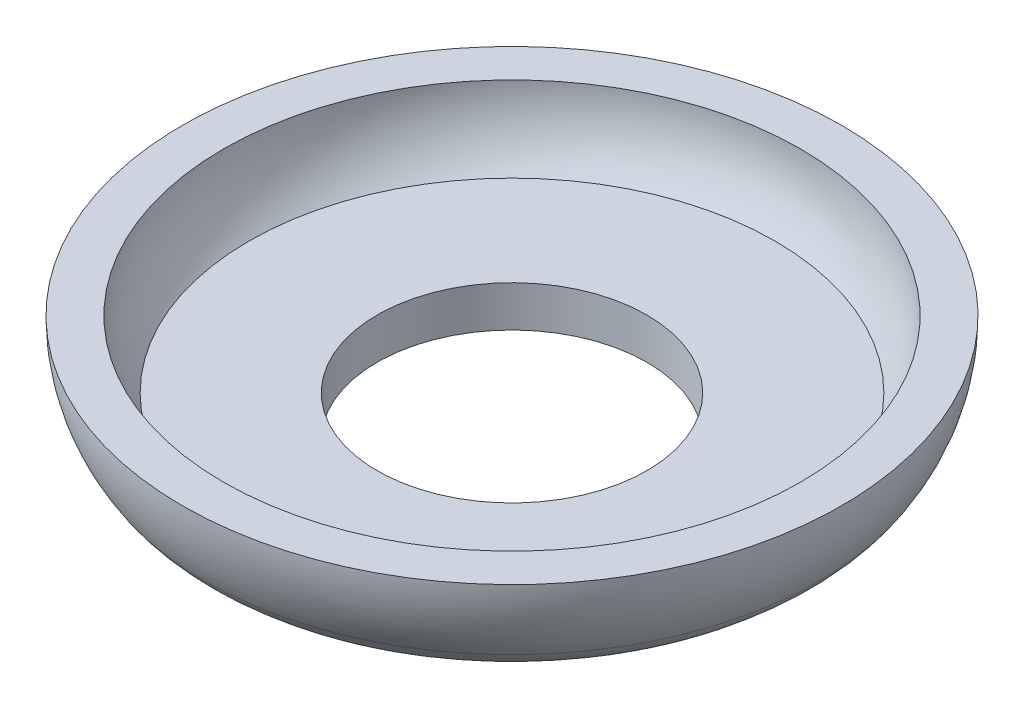
SolidWorks part; units mm, degrees
material "Cast Carbon Steel"
ref_plane "Front" through (0, 0, 0) normal (0, 0, 1) x (1, 0, 0)
ref_plane "Top" through (0, 0, 0) normal (0, 1, 0) x (1, 0, 0)
ref_plane "Right" through (0, 0, 0) normal (1, 0, 0) x (0, 0, -1)
sketch "Sketch1" plane through (0, 0, 0) normal (0, 0, 1) x (1, 0, 0)
  line L0 (5.0165, 0) -> (9.2806, 0)
  line L1 (12.2555, 4.0132) -> (12.2555, 10.0233) construction
  line L2 (5.0165, 1.524) -> (9.779, 1.524)
  line L3 (5.0165, 1.524) -> (5.0165, 0)
  line L4 (10.7315, 4.0132) -> (12.2555, 4.0132)
  line L5 (5.0165, 0) -> (10.3918, 0) construction
  line L6 (0, 0) -> (0, 1.524) construction
  arc A0 (11.4135, 1.1606) -> (12.2555, 4.0132) centre (7.0027, 4.0132) ccw
  arc A1 (9.779, 1.524) -> (10.7315, 4.0132) centre (7.0027, 4.0132) ccw
  arc A2 (10.3918, 0) -> (12.2555, 4.0132) centre (7.0027, 4.0132) ccw construction
  arc A3 (9.2806, 0) -> (11.4135, 1.1606) centre (9.2806, 2.54) ccw
  dimension "D1" = 5.0165
  dimension "D6" = 2.54
  dimension "D2" = 7.239
  dimension "D3" = 4.0132
  dimension "D5" = 4.7625
  dimension "D4" = 1.524
revolve "Revolve1" add sketch "Sketch1" angle 360 about L6
